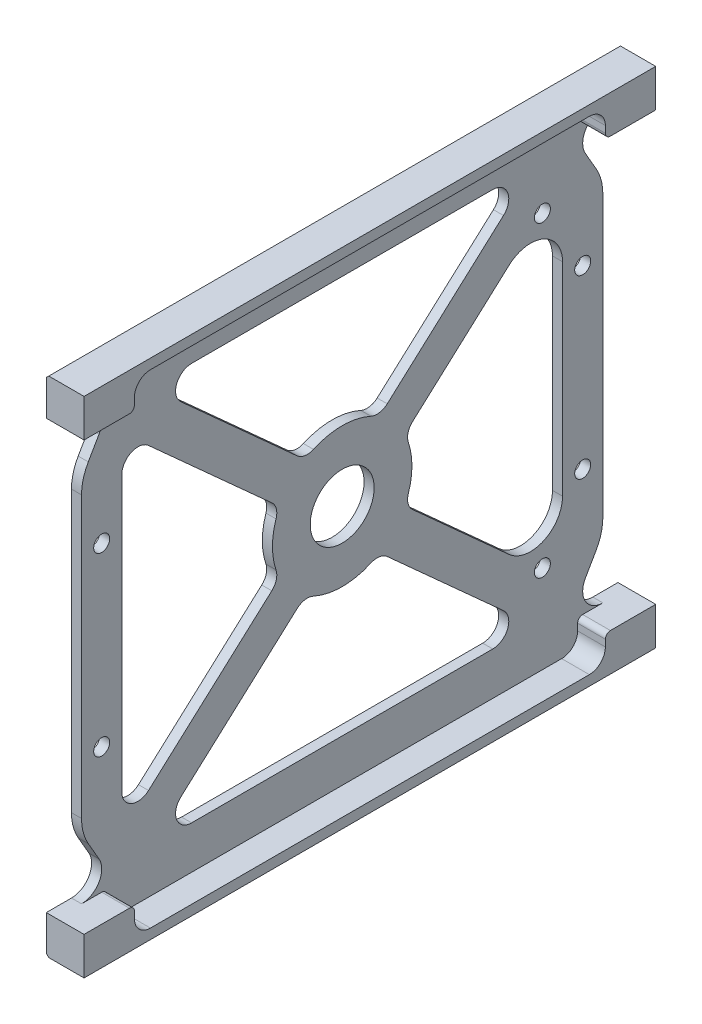
SolidWorks part; units mm, degrees
material "6061-T6 (SS)"
ref_plane "Front Plane" through (0, 0, 0) normal (0, 0, 1) x (1, 0, 0)
ref_plane "Top Plane" through (0, 0, 0) normal (0, 1, 0) x (1, 0, 0)
ref_plane "Right Plane" through (0, 0, 0) normal (1, 0, 0) x (0, 0, -1)
sketch "Sketch1" plane through (0, 0, 0) normal (0, 0, 1) x (1, 0, 0)
  line L0 (0, 50) -> (0, -50)
  line L1 (0, -50) -> (7.5, -50)
  line L2 (7.5, -50) -> (7.5, -42.5)
  line L3 (7.5, -42.5) -> (2, -42.5)
  line L4 (2, -42.5) -> (2, 42.5)
  line L5 (2, 42.5) -> (7.5, 42.5)
  line L6 (7.5, 42.5) -> (7.5, 50)
  line L7 (7.5, 50) -> (0, 50)
  dimension "D1" = 2
  dimension "D2" = 7.5
  dimension "D3" = 7.5
  dimension "D4" = 100
  dimension "D5" = 50
extrude "Boss-Extrude1" add sketch "Sketch1" along normal mid plane 113.5
sketch "Sketch2" plane through (2, 0, 0) normal (1, 0, 0) x (0, 0, -1)
  line L0 (-56.75, -42.5) -> (56.75, -42.5) construction
  line L1 (-56.75, 42.5) -> (-51.75, 42.5)
  line L2 (-56.75, 42.5) -> (-56.75, -42.5)
  line L3 (-56.75, -42.5) -> (-51.75, -42.5)
  line L4 (-51.75, 42.5) -> (-51.75, -42.5)
  line L5 (-56.75, 42.5) -> (-51.75, -42.5) construction
  line L6 (-56.75, -42.5) -> (-51.75, 42.5) construction
  line L7 (-56.75, -42.5) -> (56.75, -42.5) construction
  line L8 (56.75, 42.5) -> (51.75, 42.5)
  line L9 (56.75, 42.5) -> (56.75, -42.5)
  line L10 (56.75, -42.5) -> (51.75, -42.5)
  line L11 (51.75, 42.5) -> (51.75, -42.5)
  line L12 (56.75, 42.5) -> (51.75, -42.5) construction
  line L13 (56.75, -42.5) -> (51.75, 42.5) construction
  line L14 (47.75, 42.5) -> (47.75, -42.5) construction
  line L15 (-56.75, 42.5) -> (56.75, 42.5) construction
  line L16 (-47.75, 42.5) -> (-47.75, -42.5) construction
  line L17 (-56.75, 42.5) -> (56.75, 42.5) construction
  circle A0 centre (-47.75, 17.5) radius 1.5875
  circle A1 centre (-47.75, -17.5) radius 1.5875
  circle A2 centre (47.75, 17.5) radius 1.5875
  circle A3 centre (47.75, -17.5) radius 1.5875
  point P4 (-54.25, 0)
  point P12 (54.25, 0)
  line M1 (56.75, -42.5) -> (56.75, 42.5)
  line M2 (56.75, 42.5) -> (-56.75, 42.5)
  line M3 (-56.75, 42.5) -> (-56.75, -42.5)
  line M4 (-56.75, -42.5) -> (56.75, -42.5)
  dimension "D3" = 3.175
  dimension "D1" = 5
  dimension "D2" = 5
  dimension "D4" = 35
  dimension "D5" = 35
  dimension "D6" = 85
  dimension "D7" = 25
  dimension "D8" = 25
  dimension "D9" = 4
  dimension "D10" = 4
extrude "Cut-Extrude1" cut sketch "Sketch2" against normal blind 2 contours L4 M2 M3 M4 | L11 M2 M4 M1 | L14 A2 | L14 A2 | L14 A3 | L14 A3 | L16 A1 | L16 A1 | L16 A0 | L16 A0
sketch "Sketch3" plane through (2, 0, 0) normal (1, 0, 0) x (0, 0, -1)
  line L1 (-29.8997, -39.5) -> (29.8997, -39.5)
  line L2 (-43.75, -27.3035) -> (-43.75, 27.3035)
  line L3 (-29.8997, 39.5) -> (29.8997, 39.5)
  line L4 (43.75, -20.1594) -> (43.75, 20.1594)
  line L5 (-43.75, -39.5) -> (43.75, 39.5) construction
  line L6 (-43.75, 39.5) -> (34.7864, -31.4072) construction
  line L7 (-32.0273, 33.9684) -> (-8.9464, 13.1296)
  line L8 (-38.4473, 29.6602) -> (-13.9724, 7.5628)
  line L9 (32.0273, 33.9684) -> (8.9464, 13.1296)
  line L10 (33.1446, 24.8726) -> (13.9724, 7.5628)
  line L11 (-51.75, 42.5) -> (-51.75, -42.5)
  line L12 (-51.75, -42.5) -> (51.75, -42.5)
  line L13 (51.75, -42.5) -> (51.75, 42.5)
  line L14 (51.75, 42.5) -> (-51.75, 42.5)
  line L15 (-51.75, 42.5) -> (-51.75, -42.5) construction
  line L16 (-51.75, -42.5) -> (51.75, -42.5) construction
  line L17 (51.75, -42.5) -> (51.75, 42.5) construction
  line L18 (51.75, 42.5) -> (-51.75, 42.5) construction
  line L19 (33.1446, -24.8726) -> (13.9724, -7.5628)
  line L20 (32.0273, -33.9684) -> (8.9464, -13.1296)
  line L21 (-32.0273, -33.9684) -> (-8.9464, -13.1296)
  line L22 (-38.4473, -29.6602) -> (-13.9724, -7.5628)
  line L23 (51.75, -42.5) -> (56.75, -42.5) construction
  line L24 (-43.75, 39.5) -> (13.3825, 39.5) construction
  line L25 (-43.75, 39.5) -> (-43.75, -39.5) construction
  line L26 (-43.75, -39.5) -> (13.3825, -39.5) construction
  line L27 (43.75, 39.5) -> (43.75, -39.5) construction
  line L28 (32.1175, -39.5) -> (43.75, -39.5) construction
  line L30 (32.1175, 39.5) -> (43.75, 39.5) construction
  line L31 (39.75, 30.5) -> (39.75, -30.5) construction
  arc A0 (13.9724, 7.5628) -> (13.1372, 4.386) centre (15.9828, 5.3361) ccw
  circle A1 centre (47.75, 17.5) radius 1.5875 construction
  arc A2 (13.1372, -4.386) -> (13.9724, -7.5628) centre (15.9828, -5.3361) ccw
  circle A3 centre (0, 0) radius 6.35
  arc A4 (-13.1372, 4.386) -> (-13.1372, -4.386) centre (0, 0) ccw
  arc A5 (5.7011, 12.6222) -> (-5.7011, 12.6222) centre (0, 0) ccw
  arc A6 (13.1372, -4.386) -> (13.1372, 4.386) centre (0, 0) ccw
  arc A7 (-5.7011, -12.6222) -> (5.7011, -12.6222) centre (0, 0) ccw
  circle A8 centre (-47.75, -17.5) radius 1.5875 construction
  arc A9 (8.9464, -13.1296) -> (5.7011, -12.6222) centre (6.9359, -15.3563) ccw
  arc A10 (-5.7011, -12.6222) -> (-8.9464, -13.1296) centre (-6.9359, -15.3563) ccw
  arc A11 (-13.1372, -4.386) -> (-13.9724, -7.5628) centre (-15.9828, -5.3361) cw
  arc A12 (-13.1372, 4.386) -> (-13.9724, 7.5628) centre (-15.9828, 5.3361) ccw
  arc A13 (8.9464, 13.1296) -> (5.7011, 12.6222) centre (6.9359, 15.3563) cw
  arc A14 (-5.7011, 12.6222) -> (-8.9464, 13.1296) centre (-6.9359, 15.3563) cw
  arc A16 (43.75, 20.1594) -> (33.1446, 24.8726) centre (37.4, 20.1594) ccw
  arc A17 (43.75, -20.1594) -> (33.1446, -24.8726) centre (37.4, -20.1594) cw
  arc A19 (-29.8997, -39.5) -> (-32.0273, -33.9684) centre (-29.8997, -36.325) cw
  arc A20 (-38.4473, -29.6602) -> (-43.75, -27.3035) centre (-40.575, -27.3035) cw
  arc A21 (-43.75, 27.3035) -> (-38.4473, 29.6602) centre (-40.575, 27.3035) cw
  arc A22 (-29.8997, 39.5) -> (-32.0273, 33.9684) centre (-29.8997, 36.325) ccw
  arc A35 (29.8997, -39.5) -> (32.0273, -33.9684) centre (29.8997, -36.325) ccw
  arc A36 (32.0273, 33.9684) -> (29.8997, 39.5) centre (29.8997, 36.325) ccw
  circle A37 centre (39.75, 30.5) radius 1.5875
  circle A38 centre (39.75, -30.5) radius 1.5875
  point P0 (0, 0)
  point P40 (12.409, -6.1513)
  point P45 (-7.383, -11.7181)
  point P52 (7.383, 11.7181)
  dimension "D7" = 12.7
  dimension "D11" = 3
  dimension "D12" = 3.175
  dimension "D13" = 6.35
  dimension "D14" = 3.175
  dimension "D15" = 3.175
  dimension "D3" = 4
  dimension "D6" = 4
  dimension "D8" = 7.5
  dimension "D9" = 7.5
  dimension "D10" = 7.5
  dimension "D4" = 4
  dimension "D5" = 3
  dimension "D16" = 4
  dimension "D17" = 61
  dimension "D18" = 30.5
extrude "Cut-Extrude2" cut sketch "Sketch3" against normal through all
chamfer "Chamfer1" distance 0.5 angle 45 2 edges at (0, 50, 0) (0, -50, 0)
sketch "Sketch4" plane through (7.5, 0, 0) normal (1, 0, 0) x (0, 0, -1)
  line L5 (-56.75, -42.5) -> (56.75, -42.5) construction
  line L6 (-56.75, 42.5) -> (56.75, 42.5) construction
  line L7 (-51.75, -42.5) -> (51.75, -42.5) construction
  line L12 (-46.75, 43.5) -> (-46.75, 44.825)
  line L13 (-43.575, 48) -> (43.575, 48)
  line L14 (-56.75, -42.5) -> (-47.75, -42.5)
  line L15 (-56.75, 42.5) -> (-47.75, 42.5)
  line L16 (46.75, 44.825) -> (46.75, 43.5)
  line L17 (46.75, -43.5) -> (46.75, -44.825)
  line L18 (43.575, -48) -> (-43.575, -48)
  line L19 (-46.75, -44.825) -> (-46.75, -43.5)
  line L20 (-56.75, 50) -> (56.75, 50) construction
  line L21 (-56.75, -50) -> (56.75, -50) construction
  line L22 (47.75, 42.5) -> (56.75, 42.5)
  line L23 (47.75, -42.5) -> (56.75, -42.5)
  line L24 (-47.75, 42.5) -> (47.75, 42.5)
  line L25 (47.75, -42.5) -> (-47.75, -42.5)
  arc A0 (47.75, 42.5) -> (46.75, 43.5) centre (47.75, 43.5) cw
  arc A1 (-46.75, 43.5) -> (-47.75, 42.5) centre (-47.75, 43.5) cw
  arc A2 (47.75, -42.5) -> (46.75, -43.5) centre (47.75, -43.5) ccw
  arc A3 (-46.75, -43.5) -> (-47.75, -42.5) centre (-47.75, -43.5) ccw
  arc A4 (-43.575, -48) -> (-46.75, -44.825) centre (-43.575, -44.825) cw
  arc A5 (43.575, -48) -> (46.75, -44.825) centre (43.575, -44.825) ccw
  arc A6 (46.75, 44.825) -> (43.575, 48) centre (43.575, 44.825) ccw
  arc A7 (-43.575, 48) -> (-46.75, 44.825) centre (-43.575, 44.825) ccw
  point P24 (46.75, 42.5)
  point P27 (-46.75, 42.5)
  point P30 (46.75, -42.5)
  point P33 (-46.75, -42.5)
  line M16 (-56.75, 42.5) -> (56.75, 42.5)
  dimension "D12" = 3.175
  dimension "D11" = 1
  dimension "D5" = 5
  dimension "D6" = 5
  dimension "D7" = 5
  dimension "D8" = 5
  dimension "D9" = 2
  dimension "D10" = 2
extrude "Cut-Extrude3" cut sketch "Sketch4" against normal up to surface (5.5 mm away) contours L18 A5 L17 A2 L25 A3 L19 A4 | L13 A7 L12 A1 A0 L16 A6 M16 up to face at (2, 0, 27.4889)
sketch "Sketch5" plane through (0, 0, 0) normal (-1, 0, 0) x (0, 0, 1)
  line L0 (-56.75, 42.5) -> (-51.75, 42.5) construction
  line L5 (-50.4103, 32.8205) -> (-48.2859, 36.5)
  line L6 (-51.75, 42.5) -> (-51.75, -42.5) construction
  line L17 (-51.75, 42.5) -> (-51.75, 23.7514)
  line L19 (-51.75, -42.5) -> (-56.75, -42.5) construction
  line L25 (-48.2859, -36.5) -> (-50.4103, -32.8205)
  line L27 (-51.75, -23.3339) -> (-51.75, -42.5)
  line L30 (-51.75, 27.8205) -> (-51.75, -27.8205)
  arc A0 (-51.75, -42.5) -> (-48.2859, -36.5) centre (-51.75, -38.5) ccw
  arc A1 (-48.2859, 36.5) -> (-51.75, 42.5) centre (-51.75, 38.5) ccw
  arc A4 (-50.4103, -32.8205) -> (-51.75, -27.8205) centre (-41.75, -27.8205) cw
  arc A5 (-50.4103, 32.8205) -> (-51.75, 27.8205) centre (-41.75, 27.8205) ccw
  dimension "D2" = 4
  dimension "D5" = 30
  dimension "D6" = 10
  dimension "D1" = 30
extrude "Cut-Extrude4" cut sketch "Sketch5" against normal blind 10
mirror "Mirror1" about plane through (0, 0, 0) normal (0, 0, 1) of "Cut-Extrude4"
fillet "Fillet1" [suppressed] radius 6.35
equation "\"D3@Sketch1\"=\"D2@Sketch1\""
equation "\"D5@Sketch1\"=\"D4@Sketch1\"/2"
equation "\"D5@Sketch2\"=\"D4@Sketch2\""
equation "\"D7@Sketch2\"=(\"D6@Sketch2\"-\"D4@Sketch2\")/2"
equation "\"D8@Sketch2\"=\"D7@Sketch2\""
equation "\"D10@Sketch2\"=\"D9@Sketch2\""
equation "\"D6@Sketch3\"=\"D4@Sketch3\""
equation "\"D9@Sketch3\"=\"D8@Sketch3\""
equation "\"D10@Sketch3\"=\"D8@Sketch3\""
equation "\"D4@Sketch3\"=\"D3@Sketch3\""
equation "\"D6@Sketch4\"=\"D5@Sketch4\""
equation "\"D7@Sketch4\"=\"D5@Sketch4\""
equation "\"D8@Sketch4\"=\"D7@Sketch4\""
equation "\"D10@Sketch4\"=\"D9@Sketch4\""
equation "\"D18@Sketch3\"=\"D17@Sketch3\"/2"
equation "\"D12@Sketch3\"=\"D14@Sketch3\""
